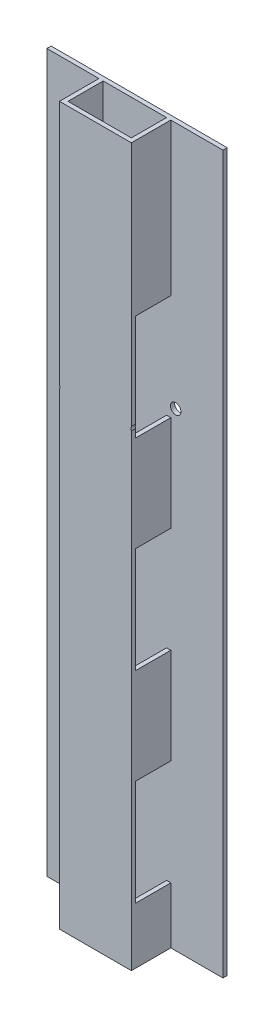
SolidWorks part; units mm, degrees
ref_plane "Alzado" through (0, 0, 0) normal (0, 0, 1) x (1, 0, 0)
ref_plane "Planta" through (0, 0, 0) normal (0, 1, 0) x (1, 0, 0)
ref_plane "Vista lateral" through (0, 0, 0) normal (1, 0, 0) x (0, 0, -1)
sketch "Croquis1" plane through (0, 0, 0) normal (0, 1, 0) x (1, 0, 0)
  line L5 (-22.5, 12.5) -> (22.5, 12.5)
  line L6 (-22.5, 12.5) -> (-22.5, -12.5)
  line L7 (-22.5, -12.5) -> (22.5, -12.5)
  line L8 (22.5, 12.5) -> (22.5, -12.5)
  line L9 (-22.5, 12.5) -> (22.5, -12.5) construction
  line L10 (-22.5, -12.5) -> (22.5, 12.5) construction
  line L11 (-25.5, -15.5) -> (25.5, -15.5)
  line L12 (-25.5, -15.5) -> (-25.5, 15.5)
  line L13 (-25.5, 15.5) -> (25.5, 15.5)
  line L14 (25.5, -15.5) -> (25.5, 15.5)
  line L15 (-25.5, -15.5) -> (25.5, 15.5) construction
  line L16 (-25.5, 15.5) -> (25.5, -15.5) construction
  point P0 (0, 0)
  point P7 (0, 0)
  dimension "D1" = 45
  dimension "D2" = 25
  dimension "D3" = 3
  dimension "D4" = 3
extrude "Saliente-Extruir2" add sketch "Croquis1" along normal mid plane 509
sketch "Croquis3" plane through (25.5, 0, 0) normal (1, 0, 0) x (0, 0, -1)
  line L0 (-64.2903, 146.5) -> (115.0822, 146.5) construction
  line L1 (-15.5, 254.5) -> (15.5, 254.5) construction
  line L2 (-64.2903, 71.5) -> (115.0822, 71.5) construction
  line L3 (-64.2903, 3.5) -> (115.0822, 3.5) construction
  line L4 (-64.2903, -71.5) -> (115.0822, -71.5) construction
  line L5 (-64.2903, -139.5) -> (115.0822, -139.5) construction
  line L6 (-64.2903, -214.5) -> (115.0822, -214.5) construction
  line L7 (-64.2903, -254.5) -> (115.0822, -254.5) construction
  line L8 (-12.5, 646.935) -> (-12.5, -393.7363) construction
  line L9 (12.5, 646.935) -> (12.5, -393.7363) construction
  line L10 (15.5, 254.5) -> (15.5, -254.5) construction
  line L11 (-15.5, 254.5) -> (-15.5, -254.5) construction
  line L13 (12.5, 146.5) -> (-12.5, 146.5)
  line L14 (12.5, 146.5) -> (12.5, 71.5)
  line L15 (12.5, 71.5) -> (-12.5, 71.5)
  line L16 (-12.5, 146.5) -> (-12.5, 71.5)
  line L17 (-12.5, 3.5) -> (12.5, 3.5)
  line L18 (-12.5, 3.5) -> (-12.5, -71.5)
  line L19 (-12.5, -71.5) -> (12.5, -71.5)
  line L20 (12.5, 3.5) -> (12.5, -71.5)
  line L21 (-12.5, -139.5) -> (12.5, -139.5)
  line L22 (-12.5, -139.5) -> (-12.5, -214.5)
  line L23 (-12.5, -214.5) -> (12.5, -214.5)
  line L24 (12.5, -139.5) -> (12.5, -214.5)
  dimension "D1" = 108
  dimension "D2" = 75
  dimension "D3" = 68
  dimension "D4" = 75
  dimension "D5" = 68
  dimension "D6" = 75
  dimension "D7" = 40
  dimension "D8" = 3
  dimension "D9" = 3
extrude "Cortar-Extruir1" cut sketch "Croquis3" against normal through all both and the other way through all
sketch "Croquis4" plane through (0, 0, -15.5) normal (0, 0, -1) x (-1, 0, 0)
  line L0 (-25.5, 254.5) -> (25.5, 254.5) construction
  line L1 (-62.5, -254.5) -> (-25.5, -254.5)
  line L2 (-62.5, -254.5) -> (-62.5, 254.5)
  line L3 (-62.5, 254.5) -> (-25.5, 254.5)
  line L4 (62.5, -254.5) -> (62.5, 254.5)
  line L5 (-25.5, -254.5) -> (25.5, -254.5) construction
  line L7 (25.5, 254.5) -> (25.5, -254.5) construction
  line L8 (-25.5, 254.5) -> (-25.5, -254.5) construction
  line L9 (-25.5, 254.5) -> (-25.5, -254.5)
  line L10 (25.5, 254.5) -> (25.5, -254.5)
  line L11 (25.5, 254.5) -> (62.5, 254.5)
  line L12 (25.5, -254.5) -> (62.5, -254.5)
  dimension "D1" = 125
  dimension "D2" = 37
extrude "Saliente-Extruir3" add sketch "Croquis4" against normal blind 3
sketch "Croquis5" plane through (0, 0, -12.5) normal (0, 0, 1) x (1, 0, 0)
  line L0 (22.5, 71.5) -> (25.5, 71.5) construction
  line L1 (22.5, 146.5) -> (25.5, 146.5) construction
  line L2 (22.5, 71.5) -> (25.5, 71.5) construction
  line L3 (22.5, 146.5) -> (25.5, 146.5) construction
  line L4 (-25.5, 71.5) -> (-22.5, 71.5) construction
  line L5 (-25.5, 146.5) -> (-22.5, 146.5) construction
  line L6 (-25.5, 146.5) -> (-22.5, 146.5) construction
  line L7 (-25.5, 71.5) -> (-22.5, 71.5) construction
  line L8 (-25.5, 254.5) -> (-25.5, -254.5) construction
  line L9 (-30.5, 143) -> (-26.5, 143) construction
  line L10 (-30.5, 143) -> (-30.5, 73) construction
  line L11 (-30.5, 73) -> (-26.5, 73) construction
  line L12 (-26.5, 143) -> (-26.5, 73) construction
  circle A0 centre (-29, 78.6937) radius 3.75
  dimension "D6" = 7.5
  dimension "D1" = 75
  dimension "D2" = 70
  dimension "D3" = 4
  dimension "D4" = 1.5
  dimension "D5" = 1
  dimension "D7" = 3.5
  dimension "D8" = 8
extrude "Cortar-Extruir2" cut sketch "Croquis5" against normal through all both and the other way through all contours A0
mirror "Simetría1" about plane through (0, 0, 0) normal (1, 0, 0) of "Cortar-Extruir2"
